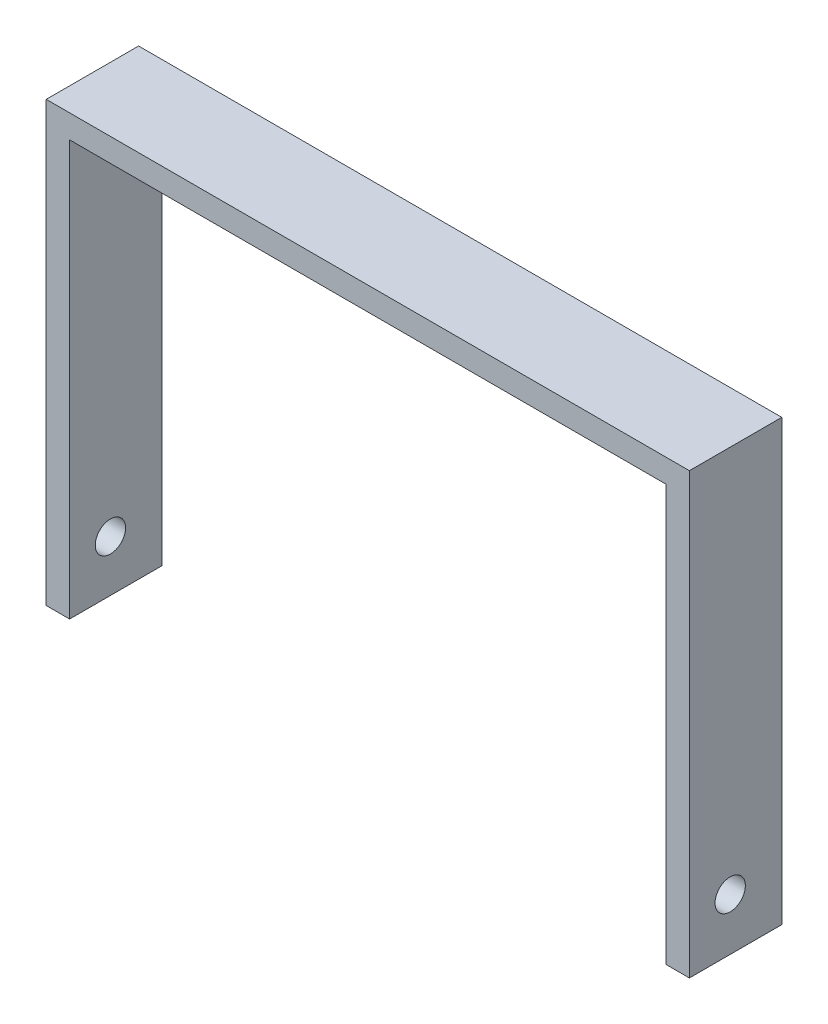
SolidWorks part; units mm, degrees
ref_plane "Front Plane" through (0, 0, 0) normal (0, 0, 1) x (1, 0, 0)
ref_plane "Top Plane" through (0, 0, 0) normal (0, 1, 0) x (1, 0, 0)
ref_plane "Right Plane" through (0, 0, 0) normal (1, 0, 0) x (0, 0, -1)
sketch "Sketch2" plane through (0, 0, 0) normal (0, 0, 1) x (1, 0, 0)
  line L1 (-29.7635, 52.7875) -> (-29.7635, -42.435)
  line L2 (-29.7635, -42.435) -> (-24.6835, -42.435)
  line L3 (-24.6835, -42.435) -> (-24.6835, 47.7075)
  line L4 (-24.6835, 47.7075) -> (104.8565, 47.7075)
  line L5 (104.8565, 47.7075) -> (104.8565, -42.6425)
  line L6 (104.8565, -42.6425) -> (109.9365, -42.6425)
  line L7 (109.9365, -42.6425) -> (109.9365, 52.7875)
  line L9 (109.9365, 52.7875) -> (-29.7635, 52.7875)
  dimension "D1" = 5.08
  dimension "D2" = 5.08
  dimension "D3" = 139.7
  dimension "D4" = 95.2225
  dimension "D5" = 5.08
extrude "Boss-Extrude4" add sketch "Sketch2" along normal blind 20.066 contours L9 L1 L2 L3 L4 L5 L6 L7
sketch "Sketch7" plane through (0, 52.7875, 0) normal (0, 1, 0) x (1, 0, 0)
  line L0 (40.0865, 0) -> (40.0865, -20.066) construction
  line L1 (109.9365, 0) -> (-29.7635, 0) construction
  line L2 (109.9365, -20.066) -> (-29.7635, -20.066) construction
  line L3 (84.5365, 0) -> (84.5365, -20.066) construction
  line L4 (-4.3635, 0) -> (-4.3635, -20.066) construction
  circle A0 centre (40.0865, -10.033) radius 7.11
  circle A1 centre (-4.3635, -10.033) radius 5.5
  circle A2 centre (84.5365, -10.033) radius 5.5
  dimension "D1" = 44.45
  dimension "D2" = 44.45
sketch "Sketch15" plane through (-29.7635, 0, 0) normal (-1, 0, 0) x (0, 0, 1)
  line L0 (11.2034, -28.1653) -> (11.2034, -34.5053) construction
  circle A0 centre (11.2034, -31.3353) radius 3.2932
extrude "Cut-Extrude4" cut sketch "Sketch15" against normal blind 181.61
ref_plane "Plane1" through (-29.7635, -28.1653, 9.1092) normal (0, 0, -1) x (-1, 0, 0)
sketch "Sketch16" plane through (-29.7635, -28.1653, 9.1092) normal (0, 0, -1) x (-1, 0, 0)
